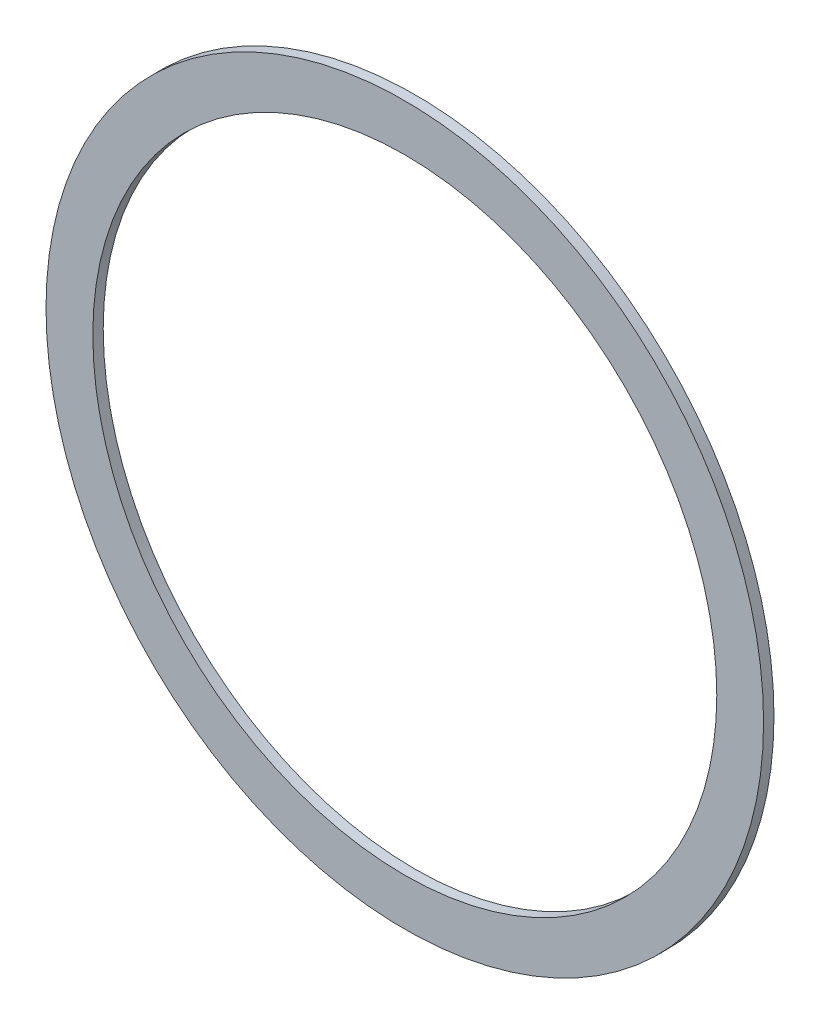
SolidWorks part; units mm, degrees
ref_plane "Front Plane" through (0, 0, 0) normal (0, 0, 1) x (1, 0, 0)
ref_plane "Top Plane" through (0, 0, 0) normal (0, 1, 0) x (1, 0, 0)
ref_plane "Right Plane" through (0, 0, 0) normal (1, 0, 0) x (0, 0, -1)
sketch "Sketch1" plane through (0, 0, 0) normal (0, 0, 1) x (1, 0, 0)
  circle A0 centre (0, 0) radius 60
  circle A1 centre (0, 0) radius 69
  dimension "D1" = 138
  dimension "D2" = 120
extrude "Boss-Extrude1" add sketch "Sketch1" along normal mid plane 2
